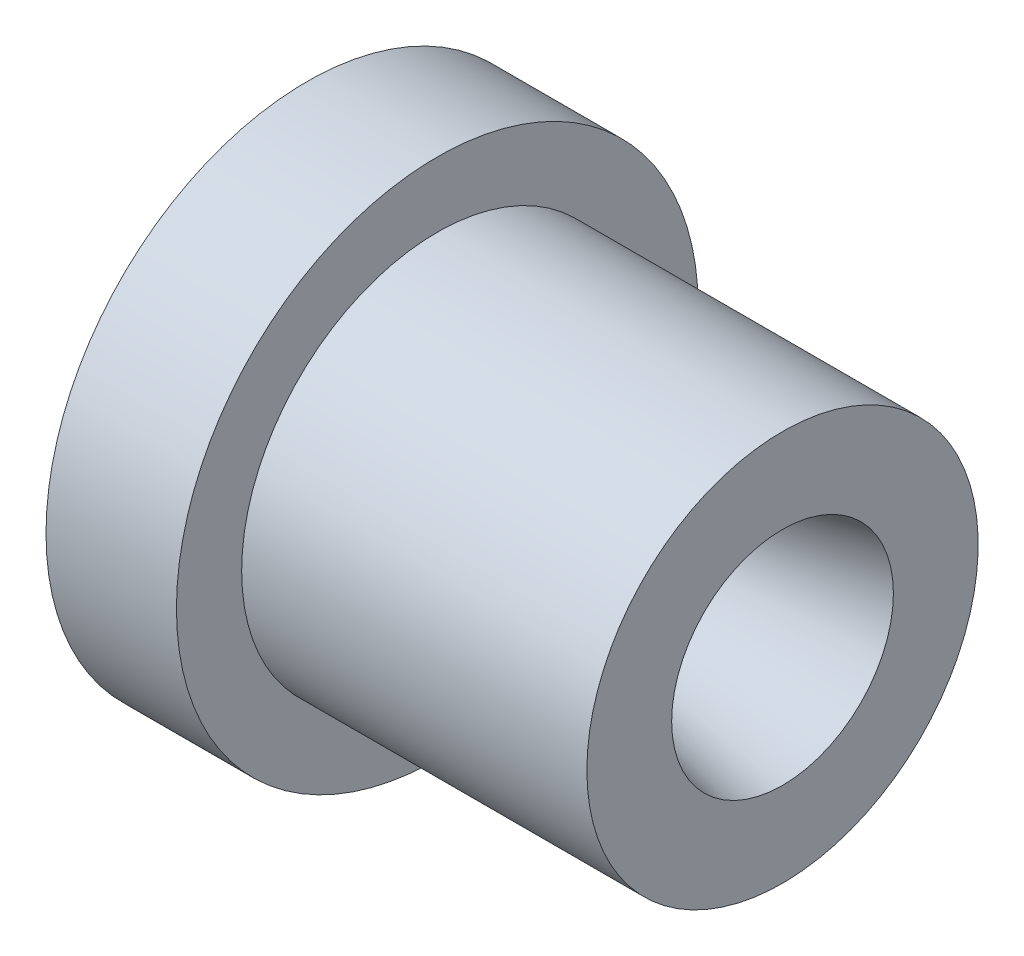
SolidWorks part; units mm, degrees
ref_plane "Front Plane" through (0, 0, 0) normal (0, 0, 1) x (1, 0, 0)
ref_plane "Top Plane" through (0, 0, 0) normal (0, 1, 0) x (1, 0, 0)
ref_plane "Right Plane" through (0, 0, 0) normal (1, 0, 0) x (0, 0, -1)
sketch "Sketch4" plane through (0, 0, 0) normal (0, 0, 1) x (1, 0, 0)
  line L0 (-30.3012, 0) -> (34.3373, 0) construction
  line L1 (-10, 20) -> (0, 20)
  line L2 (0, 20) -> (0, 15)
  line L3 (0, 15) -> (26.4662, 15)
  line L4 (-10, 20) -> (-10, 15)
  line L5 (-10, 15) -> (0, 5)
  line L6 (0, 5) -> (10, 5)
  line L7 (10, 5) -> (26.4662, 8.5)
  line L8 (26.4662, 8.5) -> (26.4662, 15)
  point P10 (0, 0)
  dimension "D1" = 10
  dimension "D2" = 40
  dimension "D3" = 45
  dimension "D4" = 12
  dimension "D5" = 10
  dimension "D6" = 10
  dimension "D7" = 17
  dimension "D8" = 30
revolve "Revolve1" add sketch "Sketch4" angle 360 about L0
